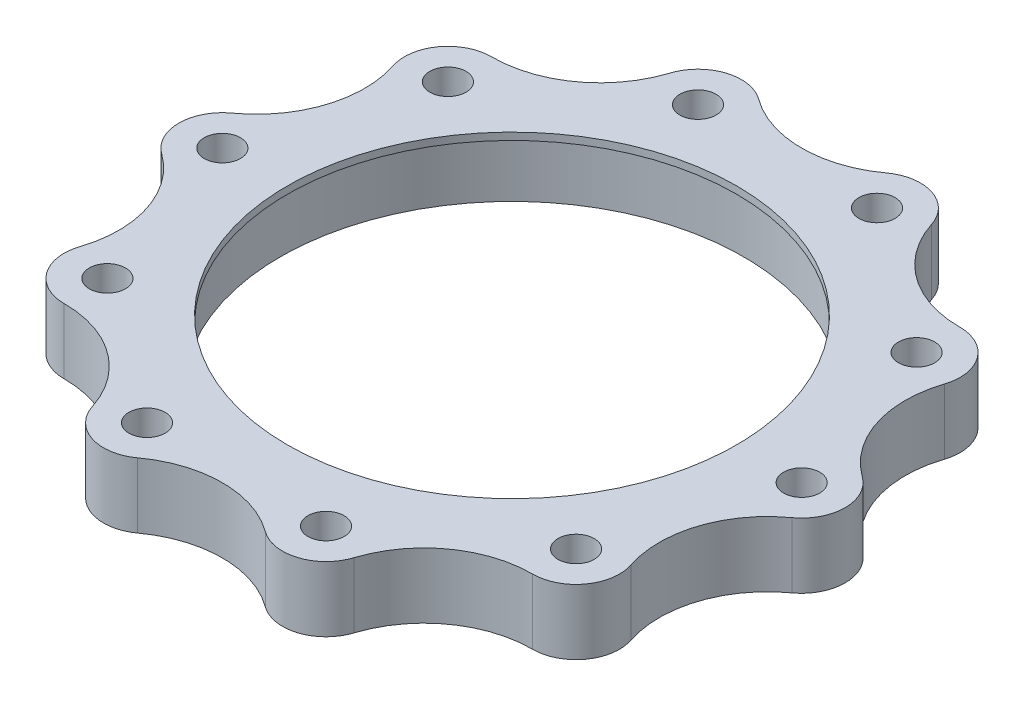
SolidWorks part; units mm, degrees
ref_plane "前视基准面" through (0, 0, 0) normal (0, 0, 1) x (1, 0, 0)
ref_plane "上视基准面" through (0, 0, 0) normal (0, 1, 0) x (1, 0, 0)
ref_plane "右视基准面" through (0, 0, 0) normal (1, 0, 0) x (0, 0, -1)
sketch "草图1" plane through (0, 0, 0) normal (0, 1, 0) x (1, 0, 0)
  circle A0 centre (0, 0) radius 20 construction
  arc A1 (21.7541, -2.4337) -> (21.7541, 2.4337) centre (20, 0) ccw
  arc A2 (16.1689, -14.7557) -> (19.03, -10.8178) centre (16.1803, -11.7557) ccw
  arc A3 (4.4078, -21.4414) -> (9.037, -19.9373) centre (6.1803, -19.0211) ccw
  arc A4 (-9.037, -19.9373) -> (-4.4078, -21.4414) centre (-6.1803, -19.0211) ccw
  arc A5 (-19.03, -10.8178) -> (-16.1689, -14.7557) centre (-16.1803, -11.7557) ccw
  arc A6 (-21.7541, 2.4337) -> (-21.7541, -2.4337) centre (-20, 0) ccw
  arc A7 (-16.1689, 14.7557) -> (-19.03, 10.8178) centre (-16.1803, 11.7557) ccw
  arc A8 (-4.4078, 21.4414) -> (-9.037, 19.9373) centre (-6.1803, 19.0211) ccw
  arc A9 (9.037, 19.9373) -> (4.4078, 21.4414) centre (6.1803, 19.0211) ccw
  arc A10 (19.03, 10.8178) -> (16.1689, 14.7557) centre (16.1803, 11.7557) ccw
  arc A11 (19.03, 10.8178) -> (21.7541, 2.4337) centre (26.1159, 8.4856) ccw
  arc A12 (21.7541, -2.4337) -> (19.03, -10.8178) centre (26.1159, -8.4856) ccw
  arc A13 (16.1689, -14.7557) -> (9.037, -19.9373) centre (16.1405, -22.2155) ccw
  arc A14 (4.4078, -21.4414) -> (-4.4078, -21.4414) centre (0, -27.4599) ccw
  arc A15 (-9.037, -19.9373) -> (-16.1689, -14.7557) centre (-16.1405, -22.2155) ccw
  arc A16 (-19.03, -10.8178) -> (-21.7541, -2.4337) centre (-26.1159, -8.4856) ccw
  arc A17 (-21.7541, 2.4337) -> (-19.03, 10.8178) centre (-26.1159, 8.4856) ccw
  arc A18 (-16.1689, 14.7557) -> (-9.037, 19.9373) centre (-16.1405, 22.2155) ccw
  arc A19 (-4.4078, 21.4414) -> (4.4078, 21.4414) centre (0, 27.4599) ccw
  arc A20 (9.037, 19.9373) -> (16.1689, 14.7557) centre (16.1405, 22.2155) ccw
  circle A21 centre (20, 0) radius 1.25
  circle A22 centre (16.1803, -11.7557) radius 1.25
  circle A23 centre (6.1803, -19.0211) radius 1.25
  circle A24 centre (-6.1803, -19.0211) radius 1.25
  circle A25 centre (-16.1803, -11.7557) radius 1.25
  circle A26 centre (-20, 0) radius 1.25
  circle A27 centre (-16.1803, 11.7557) radius 1.25
  circle A28 centre (-6.1803, 19.0211) radius 1.25
  circle A29 centre (6.1803, 19.0211) radius 1.25
  circle A30 centre (16.1803, 11.7557) radius 1.25
  circle A31 centre (0, 0) radius 5 construction
  circle A32 centre (10, 0) radius 2.25 construction
  circle A33 centre (0, 0) radius 16
  point P26 (0, 0)
  point P57 (0, 0)
  point P67 (0, 0)
  dimension "D1" = 40
  dimension "D2" = 6
  dimension "D5" = 2.5
  dimension "D7" = 10
  dimension "D8" = 4.5
  dimension "D9" = 10
  dimension "D10" = 32
  dimension "D3" = 10
  dimension "D4" = 10
  dimension "D6" = 10
extrude "凸台-拉伸1" add sketch "草图1" along normal blind 4.5
sketch "草图2" plane through (0, 4.5, 0) normal (0, 1, 0) x (1, 0, 0)
  circle A0 centre (0, 0) radius 16 construction
  circle A1 centre (0, 0) radius 16
  circle A2 centre (0, 0) radius 15.5
  dimension "D1" = 0.5
extrude "凸台-拉伸2" add sketch "草图2" against normal blind 0.5
